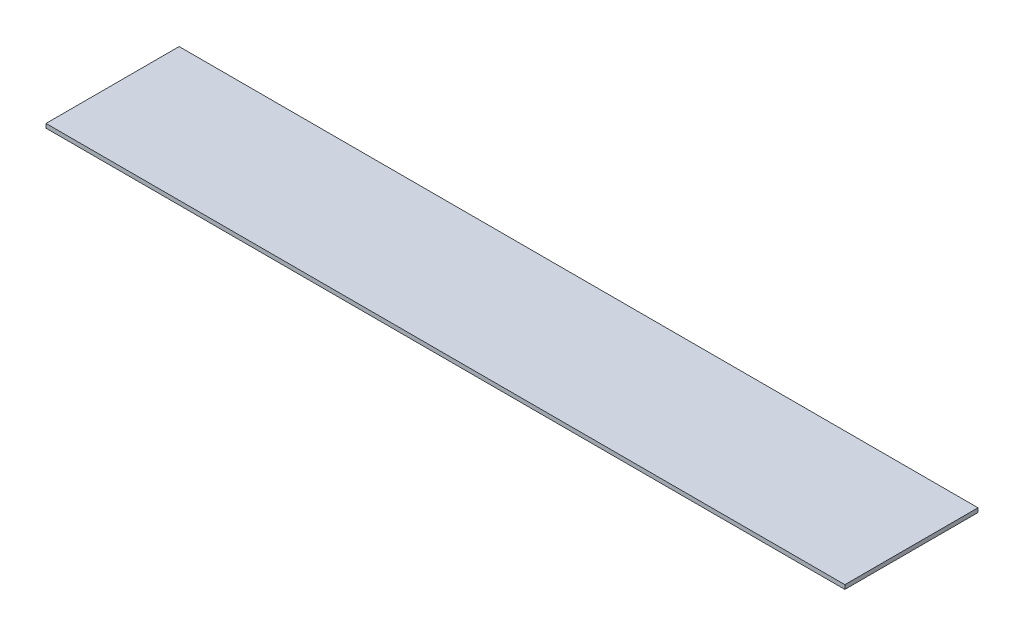
SolidWorks part; units mm, degrees
ref_plane "Front Plane" through (0, 0, 0) normal (0, 0, 1) x (1, 0, 0)
ref_plane "Top Plane" through (0, 0, 0) normal (0, 1, 0) x (1, 0, 0)
ref_plane "Right Plane" through (0, 0, 0) normal (1, 0, 0) x (0, 0, -1)
sketch "Sketch1" plane through (0, 0, 0) normal (0, 1, 0) x (1, 0, 0)
  line L1 (0, 0) -> (304.8, 0)
  line L2 (0, 0) -> (0, 50.8)
  line L3 (0, 50.8) -> (304.8, 50.8)
  line L4 (304.8, 0) -> (304.8, 50.8)
  dimension "D1" = 50.8
  dimension "D2" = 304.8
extrude "Boss-Extrude1" add sketch "Sketch1" along normal blind 1.5875
